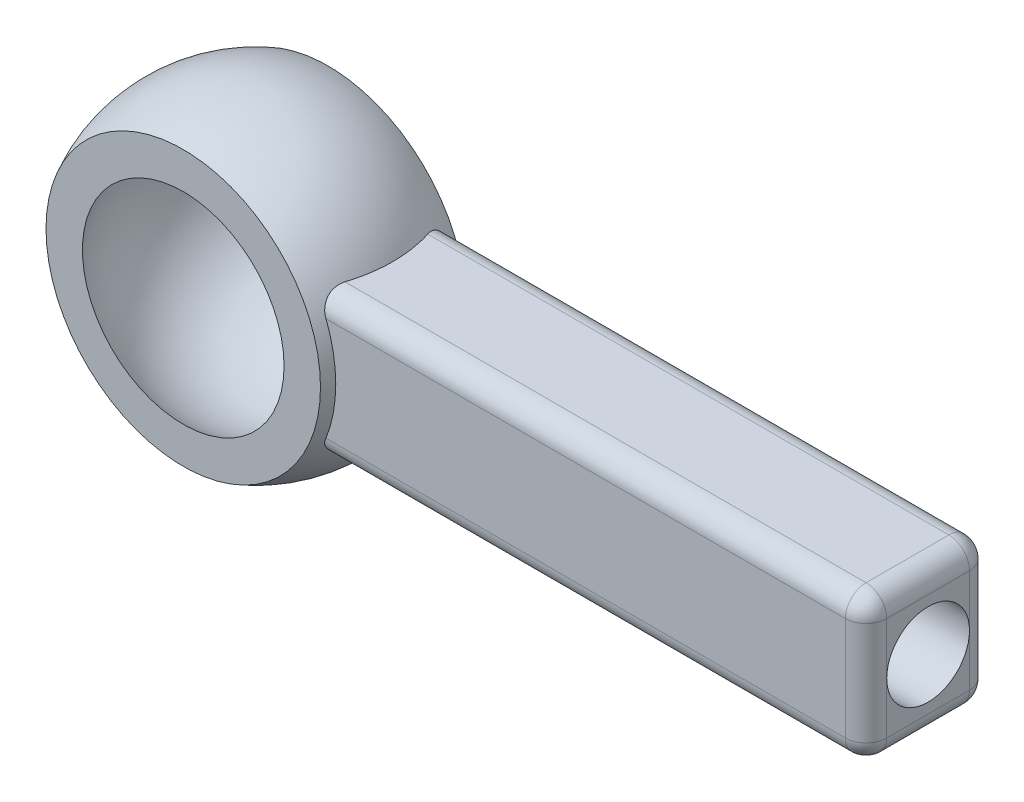
SolidWorks part; units mm, degrees
ref_plane "前视基准面" through (0, 0, 0) normal (0, 0, 1) x (1, 0, 0)
ref_plane "上视基准面" through (0, 0, 0) normal (0, 1, 0) x (1, 0, 0)
ref_plane "右视基准面" through (0, 0, 0) normal (1, 0, 0) x (0, 0, -1)
other "Configuration Table"
sketch "草图1" plane through (0, 0, 0) normal (0, 1, 0) x (1, 0, 0)
  line L0 (0, -116.1169) -> (0, 5689.7285) construction
  line L1 (-3, 0) -> (-3.75, 0) construction
  line L2 (-2.4367, 1.75) -> (-3.3166, 1.75)
  line L3 (-2.4367, -1.75) -> (-3.3166, -1.75)
  line L4 (0, 1.75) -> (-2.4367, 1.75) construction
  line L5 (0, 0) -> (-3, 0) construction
  line L6 (0, -1.75) -> (-2.4367, -1.75) construction
  arc A0 (-3.3166, 1.75) -> (-3.3166, -1.75) centre (0, 0) ccw
  arc A1 (-2.4367, 1.75) -> (-2.4367, -1.75) centre (0, 0) ccw
  arc A2 (0, 3.75) -> (-3.3166, 1.75) centre (0, 0) ccw construction
  arc A3 (0, 3) -> (-2.4367, 1.75) centre (0, 0) ccw construction
  arc A4 (-2.4367, -1.75) -> (0, -3) centre (0, 0) ccw construction
  arc A5 (0, -3) -> (0, 3) centre (0, 0) ccw construction
  arc A6 (-3.3166, -1.75) -> (0, -3.75) centre (0, 0) ccw construction
  arc A7 (0, -3.75) -> (0, 3.75) centre (0, 0) ccw construction
  dimension "D1" = 6
  dimension "D2" = 7.5
  dimension "D3" = 3.5
revolve "旋转1" add sketch "草图1" angle 360 about L0
sketch "草图2" plane through (0, 0, 0) normal (0, 0, 1) x (1, 0, 0)
  line L0 (-3.75, 0) -> (16.25, 0) construction
  line L1 (16.25, -1.75) -> (16.25, 1.75)
  line L2 (16.25, 1.75) -> (3.3166, 1.75)
  line L3 (16.25, -1.75) -> (3.3166, -1.75)
  line L4 (3.3166, 1.75) -> (2.8174, 1.75)
  line L5 (3.3166, -1.75) -> (2.8174, -1.75)
  circle A0 centre (0, 0) radius 3.75 construction
  arc A1 (3.3166, 1.75) -> (3.3166, -1.75) centre (0, 0) ccw
  circle A2 centre (0, 0) radius 3.3166 construction
  circle A3 centre (0, 0) radius 3.3166
  dimension "D1" = 20
  dimension "D2" = 3.5
extrude "凸台-拉伸1" add sketch "草图2" along normal mid plane 3 separate body contours A1 L0 L1 L2 | L0 A1 L3 L1
fillet "圆角1" radius 0.5 8 edges at (16.25, 0, -1.5) (16.25, 0, 1.5) (16.25, -1.75, 0) (16.25, 1.75, 0) (9.5337, 1.75, -1.5) (9.5337, 1.75, 1.5) (9.5337, -1.75, -1.5) (9.5337, -1.75, 1.5)
sketch "草图3" plane through (16.25, 0, 0) normal (1, 0, 0) x (0, 0, -1)
  circle A0 centre (0, 0) radius 1
  dimension "D1" = 2
extrude "切除-拉伸1" cut sketch "草图3" against normal blind 5
